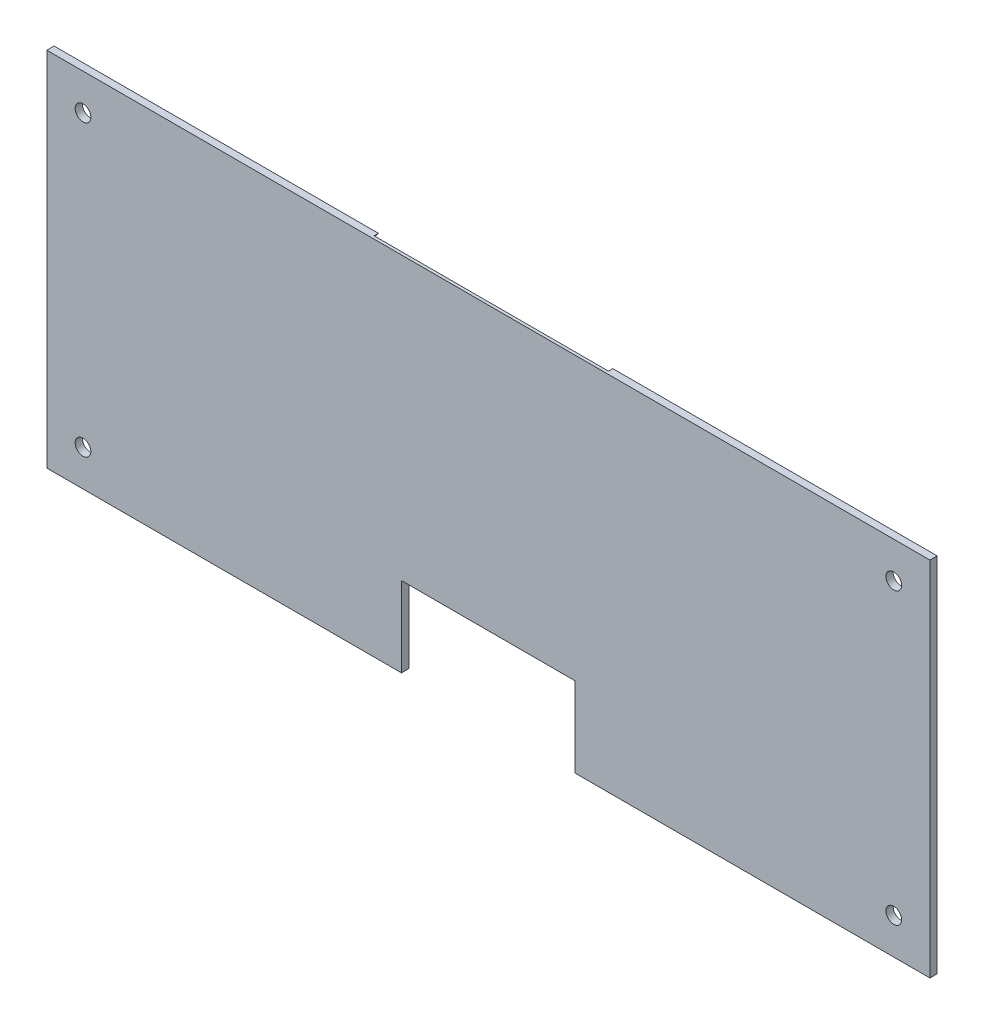
SolidWorks part; units mm, degrees
ref_plane "Front" through (0, 0, 0) normal (0, 0, 1) x (1, 0, 0)
ref_plane "Top" through (0, 0, 0) normal (0, 1, 0) x (1, 0, 0)
ref_plane "Right" through (0, 0, 0) normal (1, 0, 0) x (0, 0, -1)
sketch "Sketch1" plane through (0, 0, 0) normal (0, 0, 1) x (1, 0, 0)
  line L0 (38.1, -79.375) -> (193.675, -79.375)
  line L1 (-193.675, 79.375) -> (193.675, 79.375)
  line L2 (-193.675, 79.375) -> (-193.675, -79.375)
  line L3 (-193.675, -79.375) -> (-38.1, -79.375)
  line L4 (193.675, 79.375) -> (193.675, -79.375)
  line L5 (0, -44.323) -> (0, 79.375) construction
  line L6 (-38.1, -79.375) -> (-38.1, -44.323)
  line L7 (-38.1, -44.323) -> (38.1, -44.323)
  line L8 (38.1, -79.375) -> (38.1, -44.323)
  line L9 (-193.675, 0) -> (193.675, 0) construction
  circle A0 centre (-177.8, 63.5) radius 3.429
  circle A1 centre (177.8, 63.5) radius 3.429
  circle A2 centre (177.8, -63.5) radius 3.429
  circle A3 centre (-177.8, -63.5) radius 3.429
  point P4 (0, 79.375)
  point P6 (-193.675, 0)
  point P11 (0, -44.323)
  dimension "D7" = 6.858
  dimension "D1" = 387.35
  dimension "D2" = 158.75
  dimension "D3" = 35.052
  dimension "D4" = 76.2
  dimension "D5" = 15.875
  dimension "D6" = 15.875
extrude "Boss-Extrude1" add sketch "Sketch1" along normal blind 3.175
sketch "Sketch3" plane through (0, 0, 0) normal (0, 0, -1) x (-1, 0, 0)
  line L0 (-38.1, -79.375) -> (-193.675, -79.375) construction
  circle A0 centre (0, 34.925) radius 67.945
  dimension "D1" = 135.89
  dimension "D2" = 114.3
extrude "Cut-Extrude2" cut sketch "Sketch3" against normal blind 1.905
